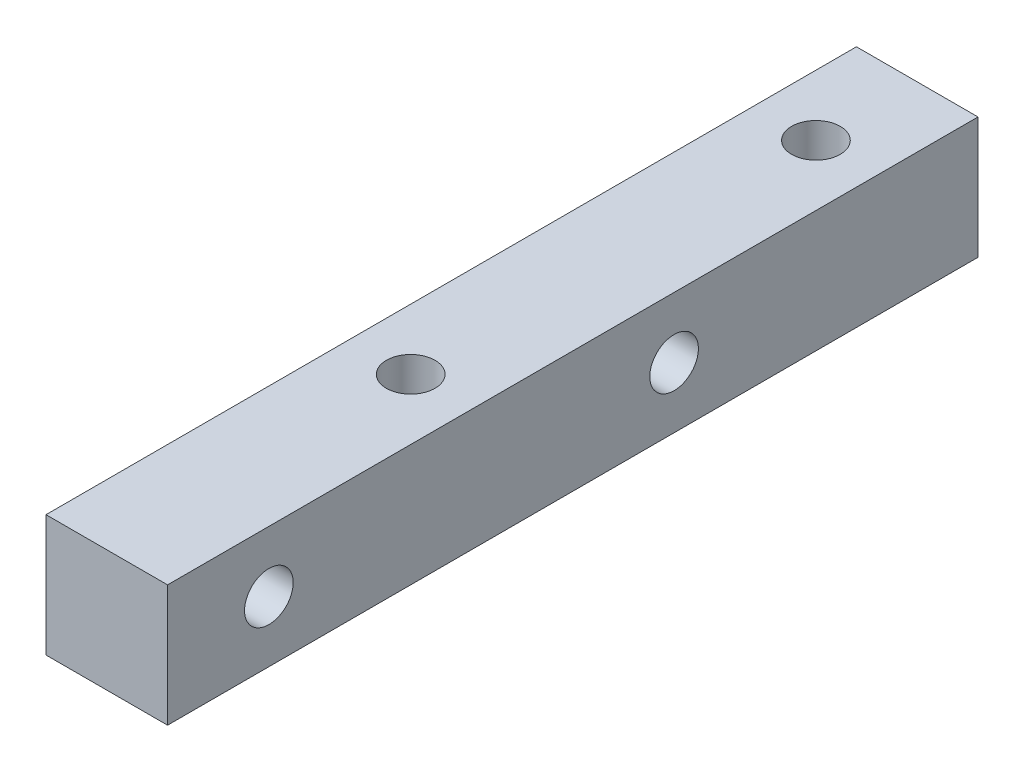
SolidWorks part; units mm, degrees
material "6061-T6 (SS)"
ref_plane "前视基准面" through (0, 0, 0) normal (0, 0, 1) x (1, 0, 0)
ref_plane "上视基准面" through (0, 0, 0) normal (0, 1, 0) x (1, 0, 0)
ref_plane "右视基准面" through (0, 0, 0) normal (1, 0, 0) x (0, 0, -1)
sketch "草图1" plane through (0, 0, 0) normal (0, 0, 1) x (1, 0, 0)
  line L1 (0, 0) -> (6, 0)
  line L2 (0, 0) -> (0, 6)
  line L3 (0, 6) -> (6, 6)
  line L4 (6, 0) -> (6, 6)
  dimension "D1" = 6
  dimension "D2" = 6
extrude "凸台-拉伸1" add sketch "草图1" along normal blind 40
sketch "草图2" plane through (0, 6, 0) normal (0, 1, 0) x (1, 0, 0)
  line L0 (3, 0) -> (3, -5) construction
  line L1 (6, 0) -> (0, 0) construction
  line L2 (3, -5) -> (3, -25) construction
  circle A0 centre (3, -5) radius 1.2
  circle A1 centre (3, -25) radius 1.2
  dimension "D1" = 2.4
  dimension "D2" = 5
  dimension "D3" = 20
extrude "切除-拉伸1" cut sketch "草图2" against normal blind 50
cosmetic thread "装饰螺纹线5"
cosmetic thread "装饰螺纹线6"
sketch "草图3" plane through (0, 0, 0) normal (-1, 0, 0) x (0, 0, 1)
  line L0 (0, 3) -> (15, 3) construction
  line L1 (0, 6) -> (0, 0) construction
  line L2 (15, 3) -> (35, 3) construction
  circle A0 centre (35, 3) radius 1.2
  circle A1 centre (15, 3) radius 1.2
  dimension "D3" = 2.4
  dimension "D1" = 15
  dimension "D2" = 20
extrude "切除-拉伸2" cut sketch "草图3" against normal blind 50
cosmetic thread "装饰螺纹线7" parameters "D2"=3
cosmetic thread "装饰螺纹线8" parameters "D2"=3
move or copy body "实体-移动/复制1" [suppressed] bodies to move or copy 108
